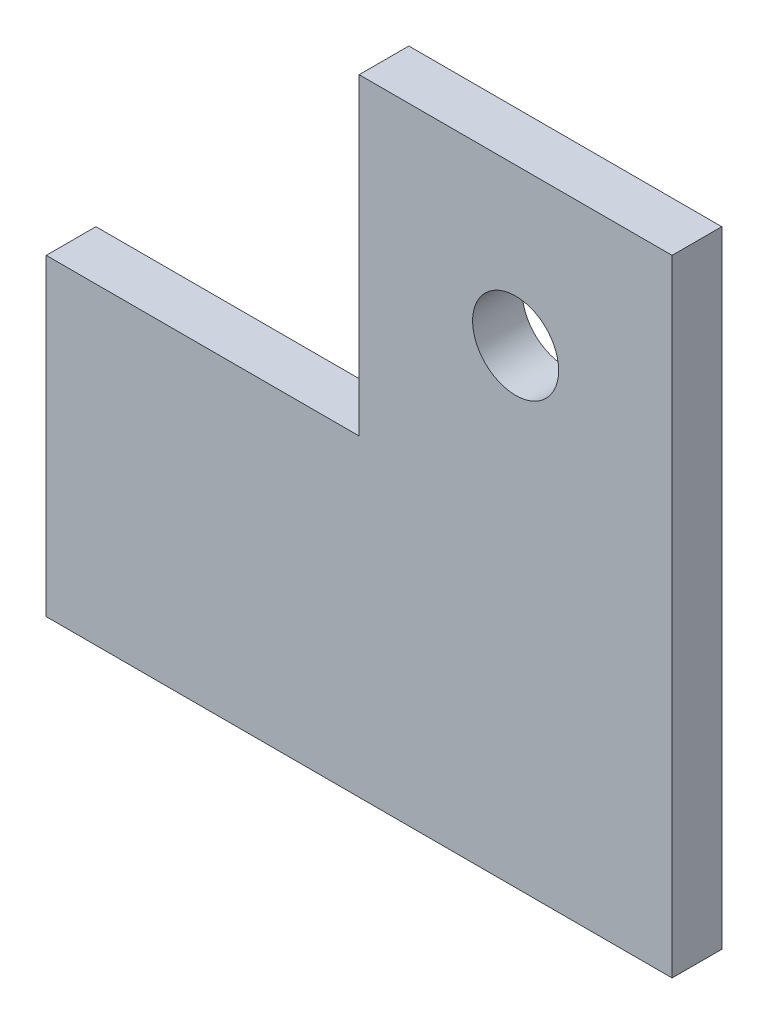
SolidWorks part; units mm, degrees
ref_plane "Front Plane" through (0, 0, 0) normal (0, 0, 1) x (1, 0, 0)
ref_plane "Top Plane" through (0, 0, 0) normal (0, 1, 0) x (1, 0, 0)
ref_plane "Right Plane" through (0, 0, 0) normal (1, 0, 0) x (0, 0, -1)
sketch "Sketch1" plane through (0, 0, 0) normal (0, 0, 1) x (1, 0, 0)
  line L0 (0, 0) -> (20, 0)
  line L1 (20, 0) -> (20, 20)
  line L3 (40, 20) -> (20, 20)
  line L4 (40, 20) -> (40, -20)
  line L5 (40, -20) -> (0, -20)
  line L6 (0, -20) -> (0, 0)
  point P6 (0, 0)
  point P9 (38.7341, 23.5993)
  dimension "D1" = 40
  dimension "D2" = 20
  dimension "D3" = 20
  dimension "D4" = 20
extrude "Boss-Extrude1" add sketch "Sketch1" along normal blind 3.175
sketch "Sketch2" plane through (0, 0, 3.175) normal (0, 0, 1) x (1, 0, 0)
  line L0 (30, 20) -> (30, -20) construction
  line L1 (40, 20) -> (20, 20) construction
  line L2 (0, -20) -> (40, -20) construction
  line L3 (20, 10) -> (40, 10) construction
  line L4 (20, 20) -> (20, 0) construction
  line L5 (40, -20) -> (40, 20) construction
  circle A0 centre (30, 10) radius 2.75
  dimension "D1" = 5.5
extrude "Cut-Extrude1" cut sketch "Sketch2" against normal up to next
